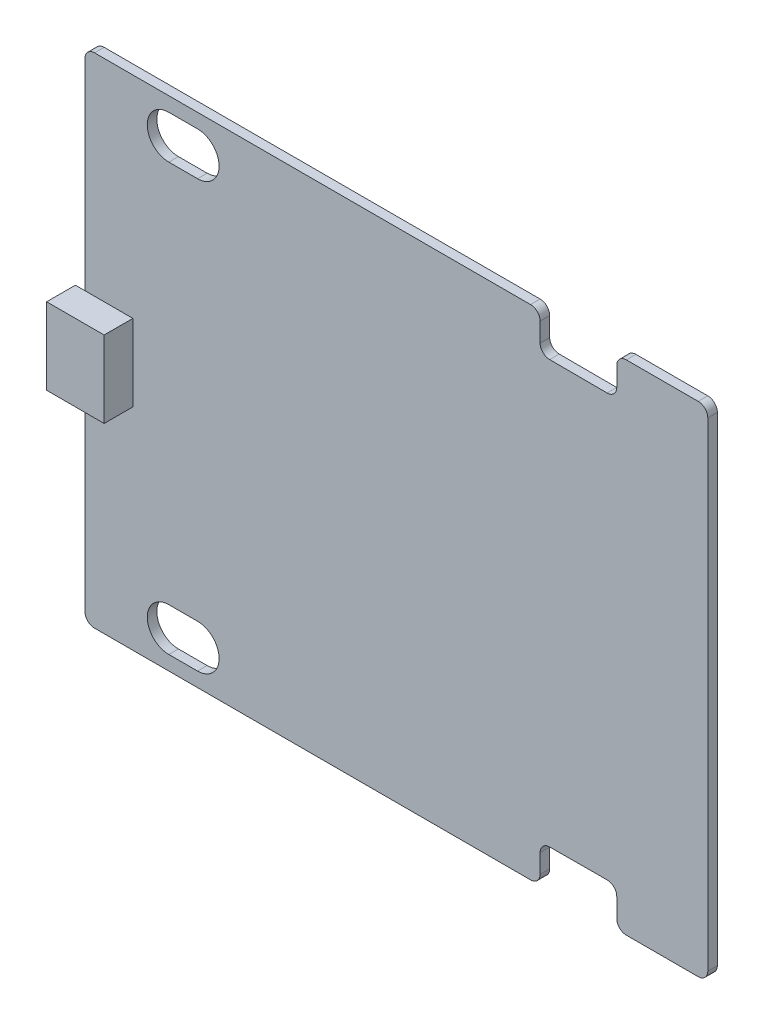
SolidWorks part; units mm, degrees
ref_plane "Спереди" through (0, 0, 0) normal (0, 0, 1) x (1, 0, 0)
ref_plane "Сверху" through (0, 0, 0) normal (0, 1, 0) x (1, 0, 0)
ref_plane "Справа" through (0, 0, 0) normal (1, 0, 0) x (0, 0, -1)
sketch "Эскиз1" plane through (0, 0, 0) normal (0, 0, 1) x (1, 0, 0)
  line L0 (-26, -26) -> (-26, 49974) construction
  line L1 (-32.5, -26) -> (32.5, -26) construction
  line L2 (-32.5, -26) -> (-32.5, 26)
  line L3 (-32.5, 26) -> (32.5, 26) construction
  line L4 (32.5, -26) -> (32.5, 26)
  line L5 (-32.5, -26) -> (32.5, 26) construction
  line L6 (-32.5, 26) -> (32.5, -26) construction
  line L7 (-56.8727, 24.5) -> (49943.1273, 24.5) construction
  line L8 (-18.5, 13.9982) -> (-18.5, 50013.9982) construction
  line L9 (-23.75, 24.5) -> (-23.75, -49975.5) construction
  line L10 (-20.75, 24.5) -> (-20.75, -49975.5) construction
  line L11 (-29.9216, 22.25) -> (49970.0784, 22.25) construction
  line L12 (-23.75, 22.25) -> (-20.75, 22.25) construction
  line L13 (-23.75, 24.5) -> (-20.75, 24.5)
  line L14 (-23.75, 20) -> (-20.75, 20)
  line L15 (0, 0) -> (-50000, 0) construction
  line L16 (-23.75, -22.25) -> (-20.75, -22.25) construction
  line L17 (-23.75, -24.5) -> (-20.75, -24.5)
  line L18 (-23.75, -20) -> (-20.75, -20)
  line L19 (23, -26) -> (23, 49974) construction
  line L20 (15, 26) -> (15, -49974) construction
  line L21 (15, 22) -> (50015, 22) construction
  line L22 (15, 26) -> (15, 22.0308)
  line L23 (15, 22.0308) -> (23, 22)
  line L24 (23, 22) -> (23, 26)
  line L25 (23, 26) -> (32.5, 26)
  line L26 (15, 26) -> (-32.5, 26)
  line L27 (-32.5, 26) -> (-32.6868, 26.0095)
  line L28 (15, -26) -> (-32.5, -26)
  line L29 (15, -26) -> (15, -22.0308)
  line L30 (15, -22.0308) -> (23, -22)
  line L31 (23, -22) -> (23, -26)
  line L32 (23, -26) -> (32.5, -26)
  arc A0 (-23.75, 24.5) -> (-23.75, 20) centre (-23.75, 22.25) ccw
  arc A1 (-20.75, 20) -> (-20.75, 24.5) centre (-20.75, 22.25) ccw
  arc A2 (-23.75, -24.5) -> (-23.75, -20) centre (-23.75, -22.25) cw
  arc A3 (-20.75, -20) -> (-20.75, -24.5) centre (-20.75, -22.25) cw
  point P0 (0, 0)
  point P20 (-22.25, 22.25)
  point P29 (-22.25, -22.25)
  dimension "D1" = 65
  dimension "D2" = 52
  dimension "D3" = 6.5
  dimension "D4" = 1.5
  dimension "D5" = 7.5
  dimension "D6" = 2.25
  dimension "D7" = 2.25
  dimension "D8" = 2.25
  dimension "D9" = 9.5
  dimension "D10" = 8
  dimension "D11" = 4
extrude "Бобышка-Вытянуть1" add sketch "Эскиз1" along normal blind 1 contours L31 L32 L4 L25 L24 L23 L22 L26 L2 L28 L29 L30 A1 L14 A0 L13 L18 A3 L17 A2
fillet "Скругление1" radius 1 12 edges at (-32.5, 26, 0.5) (-32.5, -26, 0.5) (15, -26, 0.5) (15, -22.0308, 0.5) (23, -22, 0.5) (23, -26, 0.5) (32.5, -26, 0.5) (32.5, 26, 0.5) (23, 26, 0.5) (23, 22, 0.5) (15, 22.0308, 0.5) (15, 26, 0.5)
sketch "Эскиз2" plane through (0, 0, 1) normal (0, 0, 1) x (1, 0, 0)
  line L0 (0, 0) -> (-50000, 0) construction
  line L1 (-47.2621, 4) -> (49952.7379, 4) construction
  line L3 (-33.5, 7.4119) -> (-33.5, -49992.5881) construction
  line L4 (-32.5, -25) -> (-32.5, 25) construction
  line L6 (-33.5, 4) -> (-27.5, 4)
  line L7 (-33.5, 4) -> (-33.5, -4)
  line L8 (-33.5, -4) -> (-27.5, -4)
  line L9 (-27.5, 4) -> (-27.5, -4)
  dimension "D1" = 4
  dimension "D2" = 1
  dimension "D3" = 6
  dimension "D4" = 8
extrude "Бобышка-Вытянуть2" add sketch "Эскиз2" along normal blind 3
